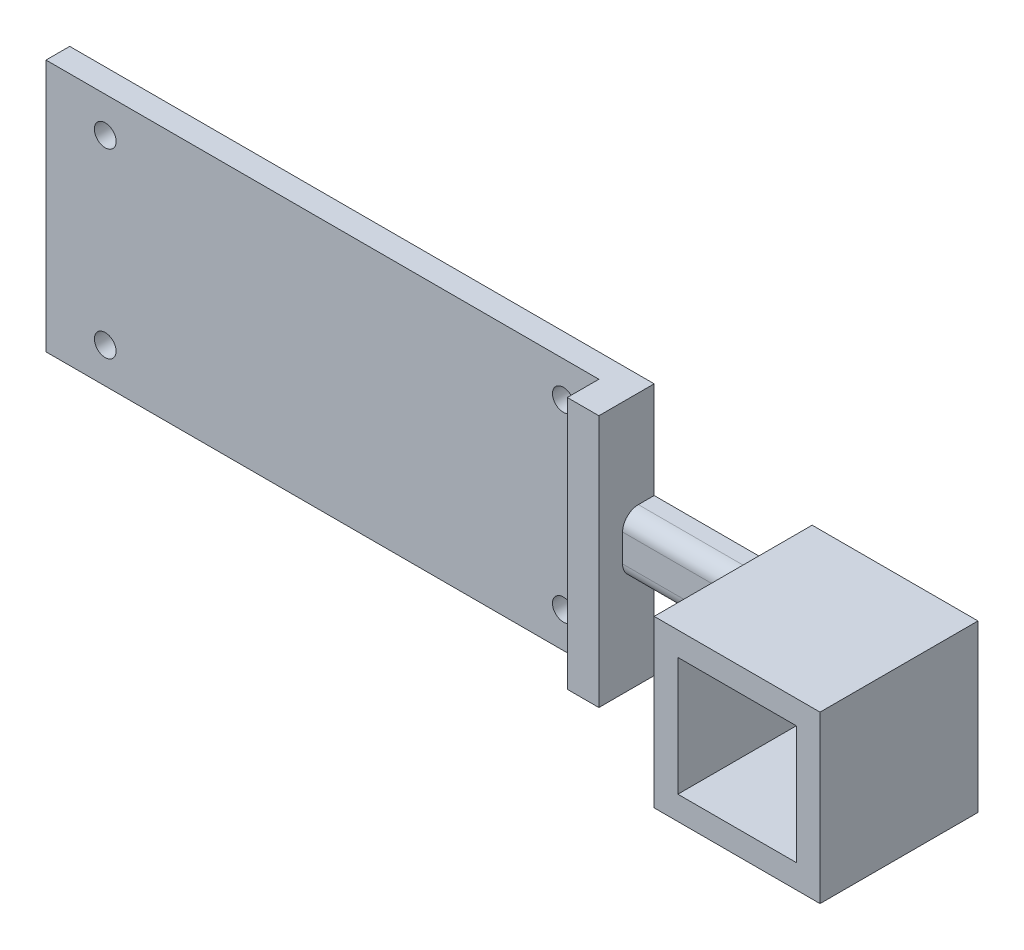
SolidWorks part; units mm, degrees
ref_plane "Front Plane" through (0, 0, 0) normal (0, 0, 1) x (1, 0, 0)
ref_plane "Top Plane" through (0, 0, 0) normal (0, 1, 0) x (1, 0, 0)
ref_plane "Right Plane" through (0, 0, 0) normal (1, 0, 0) x (0, 0, -1)
sketch "Sketch2" plane through (0, 0, 0) normal (0, 0, 1) x (1, 0, 0)
  line L1 (10.5, -10.5) -> (-10.5, -10.5)
  line L2 (10.5, -10.5) -> (10.5, 10.5)
  line L3 (10.5, 10.5) -> (-10.5, 10.5)
  line L4 (-10.5, -10.5) -> (-10.5, 10.5)
  line L5 (10.5, -10.5) -> (-10.5, 10.5) construction
  line L6 (10.5, 10.5) -> (-10.5, -10.5) construction
  point P0 (0, 0)
  dimension "D1" = 21
extrude "Boss-Extrude1" add sketch "Sketch2" along normal blind 20
sketch "Sketch3" plane through (0, 0, 20) normal (0, 0, 1) x (1, 0, 0)
  line L1 (7.5, -7.5) -> (-7.5, -7.5)
  line L2 (7.5, -7.5) -> (7.5, 7.5)
  line L3 (7.5, 7.5) -> (-7.5, 7.5)
  line L4 (-7.5, -7.5) -> (-7.5, 7.5)
  line L5 (7.5, -7.5) -> (-7.5, 7.5) construction
  line L6 (7.5, 7.5) -> (-7.5, -7.5) construction
  point P0 (0, 0)
  dimension "D1" = 15
  dimension "D2" = 15
extrude "Cut-Extrude1" cut sketch "Sketch3" against normal blind 20
sketch "Sketch4" plane through (-10.5, 0, 0) normal (-1, 0, 0) x (0, 0, 1)
  line L1 (0, 3.75) -> (4, 3.75)
  line L2 (0, 3.75) -> (0, -3.75)
  line L3 (0, -3.75) -> (4, -3.75)
  line L4 (4, 3.75) -> (4, -3.75)
  point P4 (0, 0)
  dimension "D1" = 7.5
  dimension "D2" = 4
  dimension "D3" = 10.5
extrude "Boss-Extrude2" add sketch "Sketch4" along normal blind 20
fillet "Fillet2" radius 2 2 edges at (-20.5, -3.75, 4) (-20.5, 3.75, 4)
sketch "Sketch5" plane through (-30.5, 0, 0) normal (-1, 0, 0) x (0, 0, 1)
  line L0 (0, 0) -> (4, 0) construction
  line L1 (0, -16) -> (7, -16)
  line L2 (0, -16) -> (0, 16)
  line L3 (0, 16) -> (7, 16)
  line L4 (7, -16) -> (7, 16)
  line L5 (4, -1.75) -> (4, 1.75) construction
  line L6 (0, 0) -> (7, 0) construction
  dimension "D1" = 32
  dimension "D2" = 7
extrude "Boss-Extrude3" add sketch "Sketch5" along normal blind 4
sketch "Sketch6" plane through (-34.5, 0, 0) normal (-1, 0, 0) x (0, 0, 1)
  line L0 (0, -16) -> (7, -16) construction
  line L1 (0, 16) -> (3, 16)
  line L2 (0, 16) -> (0, -16)
  line L3 (0, -16) -> (3, -16)
  line L4 (3, 16) -> (3, -16)
  dimension "D1" = 3
extrude "Boss-Extrude4" add sketch "Sketch6" along normal blind 70
sketch "Sketch8" plane through (0, 0, 3) normal (0, 0, 1) x (1, 0, 0)
  line L0 (-34.5, -16) -> (-34.5, 16) construction
  line L1 (-104.5, -16) -> (-34.5, -16) construction
  circle A0 centre (-39, -11.5) radius 1.375
  circle A1 centre (-39, 11.5) radius 1.375
  circle A2 centre (-97, -11.5) radius 1.375
  circle A3 centre (-97, 11.5) radius 1.375
  point P12 (0, 0)
  dimension "D1" = 2.75
  dimension "D2" = 2.75
  dimension "D3" = 2.75
  dimension "D4" = 2.75
  dimension "D5" = 58
  dimension "D6" = 23
  dimension "D7" = 4.5
  dimension "D8" = 4.5
  dimension "D9" = 23
extrude "Cut-Extrude2" cut sketch "Sketch8" against normal blind 4
